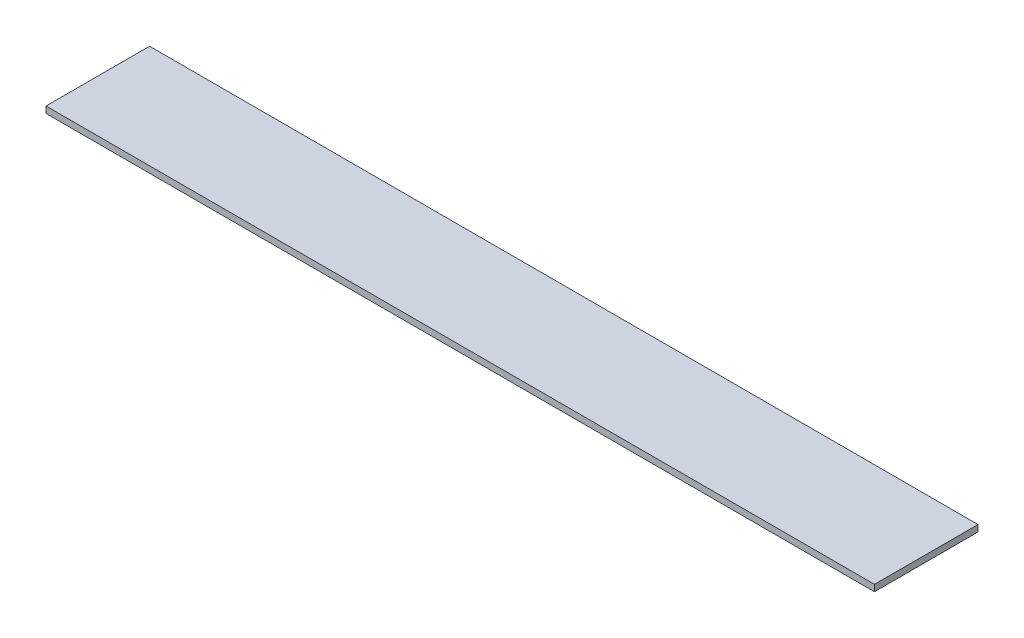
SolidWorks part; units mm, degrees
ref_plane "Front" through (0, 0, 0) normal (0, 0, 1) x (1, 0, 0)
ref_plane "Top" through (0, 0, 0) normal (0, 1, 0) x (1, 0, 0)
ref_plane "Right" through (0, 0, 0) normal (1, 0, 0) x (0, 0, -1)
sketch "Sketch1" plane through (0, 0, 0) normal (0, 1, 0) x (1, 0, 0)
  line L1 (-201.8109, 80.2954) -> (204.5891, 80.2954)
  line L2 (-201.8109, 80.2954) -> (-201.8109, 29.4954)
  line L3 (-201.8109, 29.4954) -> (204.5891, 29.4954)
  line L4 (204.5891, 80.2954) -> (204.5891, 29.4954)
  dimension "D1" = 50.8
  dimension "D2" = 406.4
extrude "Boss-Extrude1" add sketch "Sketch1" along normal blind 3.175
